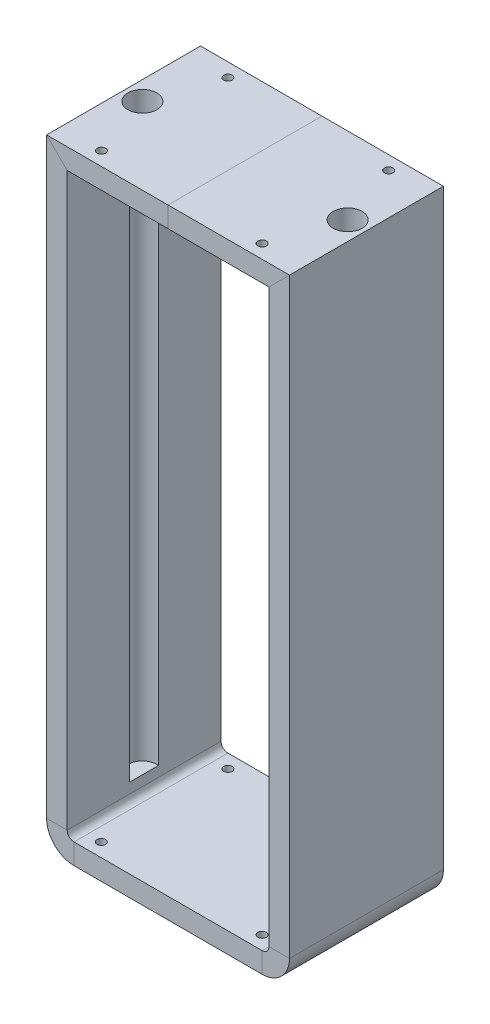
SolidWorks part; units mm, degrees
ref_plane "Front Plane" through (0, 0, 0) normal (0, 0, 1) x (1, 0, 0)
ref_plane "Top Plane" through (0, 0, 0) normal (0, 1, 0) x (1, 0, 0)
ref_plane "Right Plane" through (0, 0, 0) normal (1, 0, 0) x (0, 0, -1)
sketch "Sketch4" plane through (0, 0, 0) normal (0, 0, 1) x (1, 0, 0)
  line L0 (-65, 350) -> (-65, 10)
  line L1 (-55, 0) -> (55, 0)
  line L2 (65, 10) -> (65, 350)
  line L3 (65, 350) -> (-65, 350)
  line L4 (0, 0) -> (0, 180.0439) construction
  arc A0 (-55, 0) -> (-65, 10) centre (-55, 10) cw
  arc A1 (55, 0) -> (65, 10) centre (55, 10) ccw
  point P6 (-65, 0)
  dimension "D3" = 10
  dimension "D4" = 10
  dimension "D1" = 130
  dimension "D2" = 350
  dimension "D5" = 0
  dimension "D6" = 65
sketch "Sketch6" plane through (0, 0, 0) normal (1, 0, 0) x (0, 0, -1)
  line L0 (0, 10) -> (0, 350) construction
  line L1 (45, 356) -> (-45, 356)
  line L2 (45, 356) -> (45, 344)
  line L3 (45, 344) -> (-45, 344)
  line L4 (-45, 356) -> (-45, 344)
  line L5 (45, 356) -> (-45, 344) construction
  line L6 (45, 344) -> (-45, 356) construction
  point P0 (0, 350)
  dimension "D1" = 90
  dimension "D2" = 12
sweep "Sweep2" add profiles "Sketch6" path "Sketch4"
sketch "Sketch7" plane through (0, 356, 0) normal (0, 1, 0) x (1, 0, 0)
  line L1 (0, 45) -> (0, -45) construction
  line L2 (27.691, 0) -> (-24.1747, 0) construction
  circle A0 centre (60, 0) radius 8.5
  circle A1 centre (-60, 0) radius 8.5
  circle A2 centre (-47, -37) radius 2.5
  circle A3 centre (-47, 37) radius 2.5
  circle A4 centre (47, -37) radius 2.5
  circle A5 centre (47, 37) radius 2.5
  dimension "D1" = 17
  dimension "D3" = 5
  dimension "D2" = 60
  dimension "D4" = 37
  dimension "D5" = 47
extrude "Cut-Extrude1" cut sketch "Sketch7" against normal blind 340
sketch "Sketch8" plane through (0, 6, 0) normal (0, 1, 0) x (1, 0, 0)
  line L0 (0, 45) -> (0, -45) construction
  line L1 (0, 0) -> (0, 54.3415) construction
  line L2 (0, 0) -> (50.3525, 0) construction
  circle A0 centre (47, 37) radius 2.5
  circle A1 centre (-47, 37) radius 2.5
  circle A2 centre (-47, -37) radius 2.5
  circle A3 centre (47, -37) radius 2.5
  dimension "D1" = 5
extrude "Cut-Extrude2" cut sketch "Sketch8" against normal blind 8
